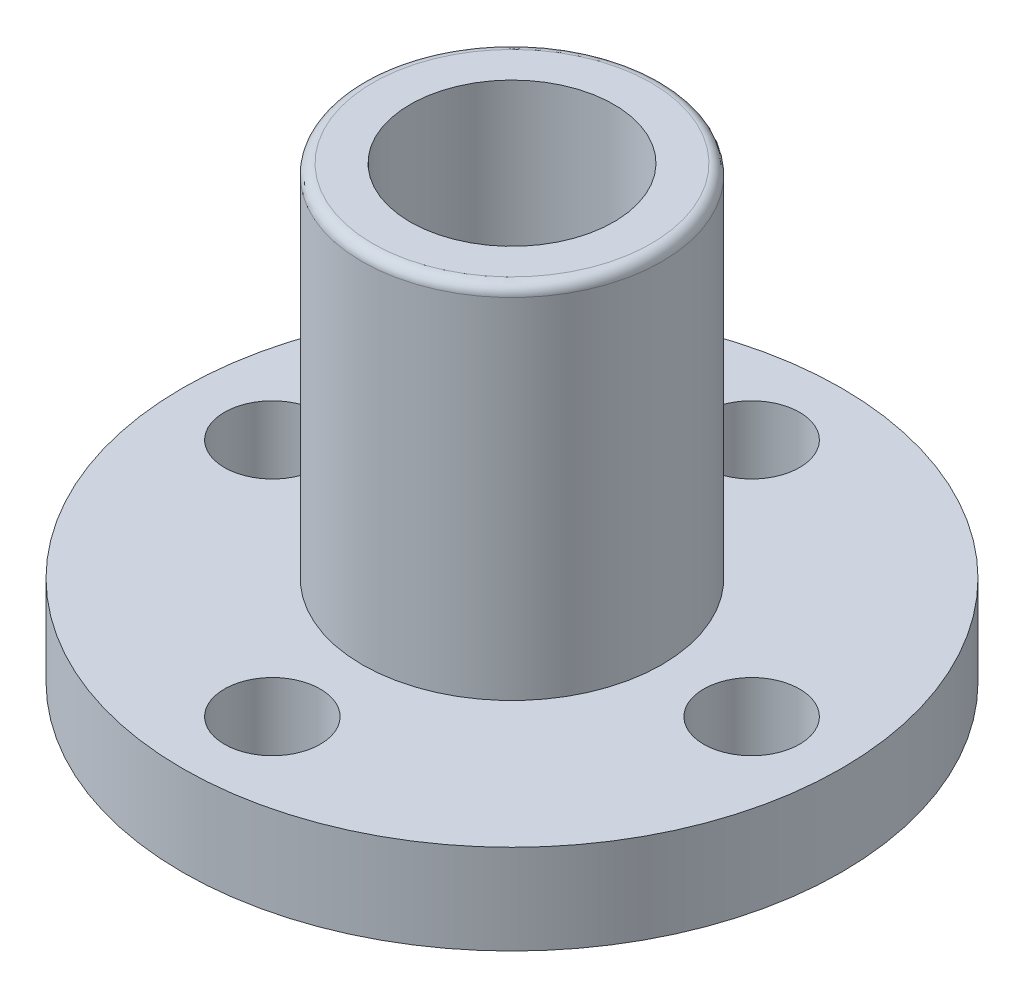
SolidWorks part; units mm, degrees
material "黄铜"
ref_plane "前视基准面" through (0, 0, 0) normal (0, 0, 1) x (1, 0, 0)
ref_plane "上视基准面" through (0, 0, 0) normal (0, 1, 0) x (1, 0, 0)
ref_plane "右视基准面" through (0, 0, 0) normal (1, 0, 0) x (0, 0, -1)
sketch "草图1" plane through (0, 0, 0) normal (0, 1, 0) x (1, 0, 0)
  circle A0 centre (0, 0) radius 11
  dimension "D1" = 22
extrude "凸台-拉伸1" add sketch "草图1" along normal blind 3
sketch "草图2" plane through (0, 3, 0) normal (0, 1, 0) x (1, 0, 0)
  circle A0 centre (0, 0) radius 5
  dimension "D1" = 10
extrude "凸台-拉伸2" add sketch "草图2" along normal blind 12
sketch "草图5" plane through (0, 3, 0) normal (0, 1, 0) x (1, 0, 0)
  circle A0 centre (0, 0) radius 8 construction
  circle A1 centre (0, 8) radius 1.6
  circle A2 centre (8, 0) radius 1.6
  circle A3 centre (0, -8) radius 1.6
  circle A4 centre (-8, 0) radius 1.6
  point P14 (0, 0)
  dimension "D1" = 16
  dimension "D2" = 3.2
  dimension "D3" = 4
extrude "切除-拉伸3" cut sketch "草图5" against normal through all
fillet "圆角1" radius 0.35 1 edges at (0, 15, 5)
sketch "草图7" plane through (0, 0, 0) normal (0, -1, 0) x (1, 0, 0)
  circle A0 centre (0, 0) radius 5
  dimension "D1" = 10
extrude "凸台-拉伸3" add sketch "草图7" along normal blind 1.5
hole_wizard "M8 螺纹孔1" positions "草图4" profile "草图3" tap size "M8" standard "GB" end condition through all
sketch "草图4" plane through (0, 15, 0) normal (0, 1, 0) x (1, 0, 0)
  point P0 (0, 0)
sketch "草图3" plane through (0, 15, 0) normal (1, 0, 0) x (0, 0, 1)
  line L0 (0, 0) -> (0, 16.5)
  line L1 (0, 16.5) -> (3.4, 16.5)
  line L2 (3.4, 16.5) -> (3.4, 0)
  line L5 (3.4, 0) -> (0, 0)
  line L11 (0, -6.35) -> (0, 107.95) construction
  dimension "通孔螺纹孔钻头直径" = 6.8
  dimension "通孔螺纹孔钻头深度" = 16.5
cosmetic thread "孔螺蚊线1" parameters "D2"=8
